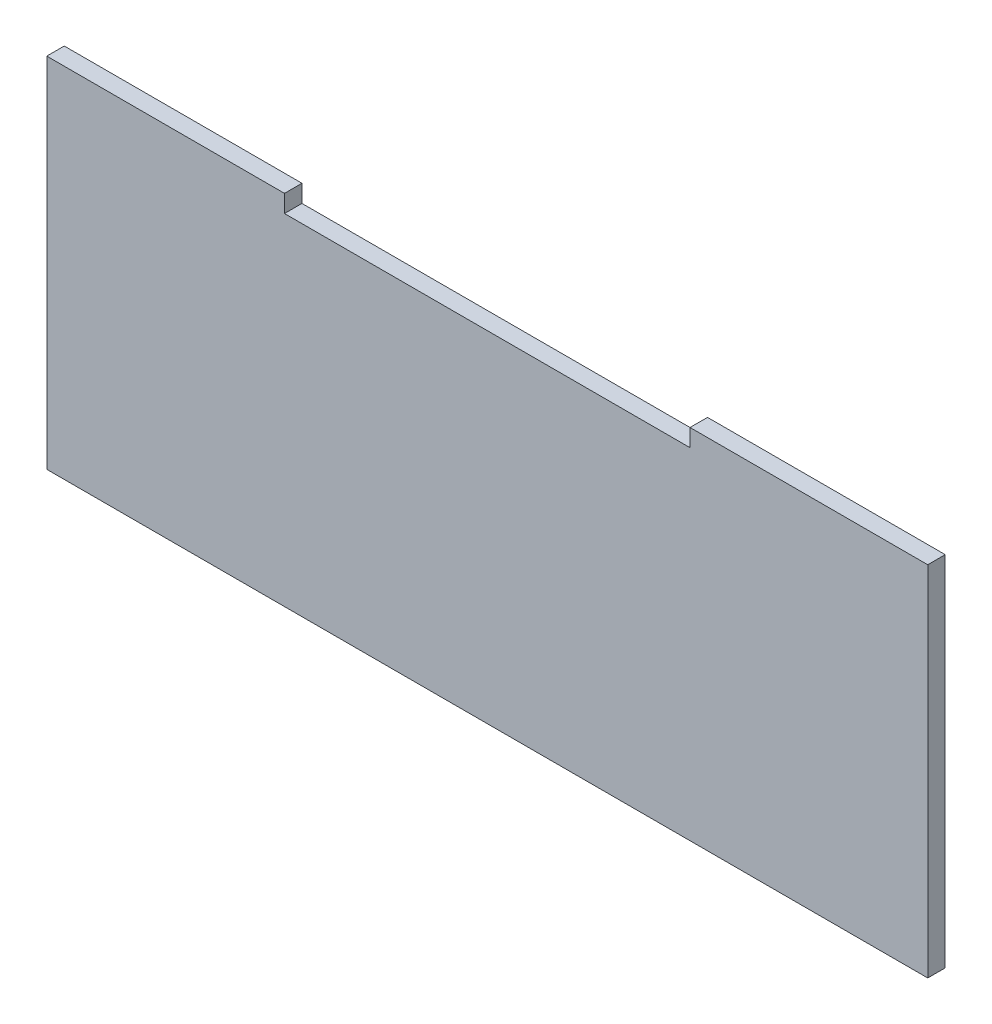
SolidWorks part; units mm, degrees
ref_plane "Front Plane" through (0, 0, 0) normal (0, 0, 1) x (1, 0, 0)
ref_plane "Top Plane" through (0, 0, 0) normal (0, 1, 0) x (1, 0, 0)
ref_plane "Right Plane" through (0, 0, 0) normal (1, 0, 0) x (0, 0, -1)
sketch "Sketch1" plane through (0, 0, 0) normal (0, 0, 1) x (1, 0, 0)
  line L0 (-98.8769, 0) -> (79.8272, 0) construction
  line L1 (0, 59.1901) -> (0, -55.108) construction
  line L2 (0, 0) -> (80, 0)
  line L3 (0, 0) -> (-80, 0)
  line L4 (-80, 0) -> (-80, 65)
  line L5 (-80, 65) -> (-36.825, 65)
  line L6 (-36.825, 65) -> (-36.825, 61.825)
  line L7 (-36.825, 61.825) -> (36.825, 61.825)
  line L8 (36.825, 61.825) -> (36.825, 65)
  line L9 (36.825, 65) -> (80, 65)
  line L10 (80, 65) -> (80, 0)
  dimension "D2" = 80
  dimension "D3" = 65
  dimension "D4" = 43.175
  dimension "D5" = 3.175
  dimension "D6" = 73.65
  dimension "D7" = 3.175
  dimension "D8" = 43.175
extrude "Boss-Extrude1" add sketch "Sketch1" along normal blind 3.175
